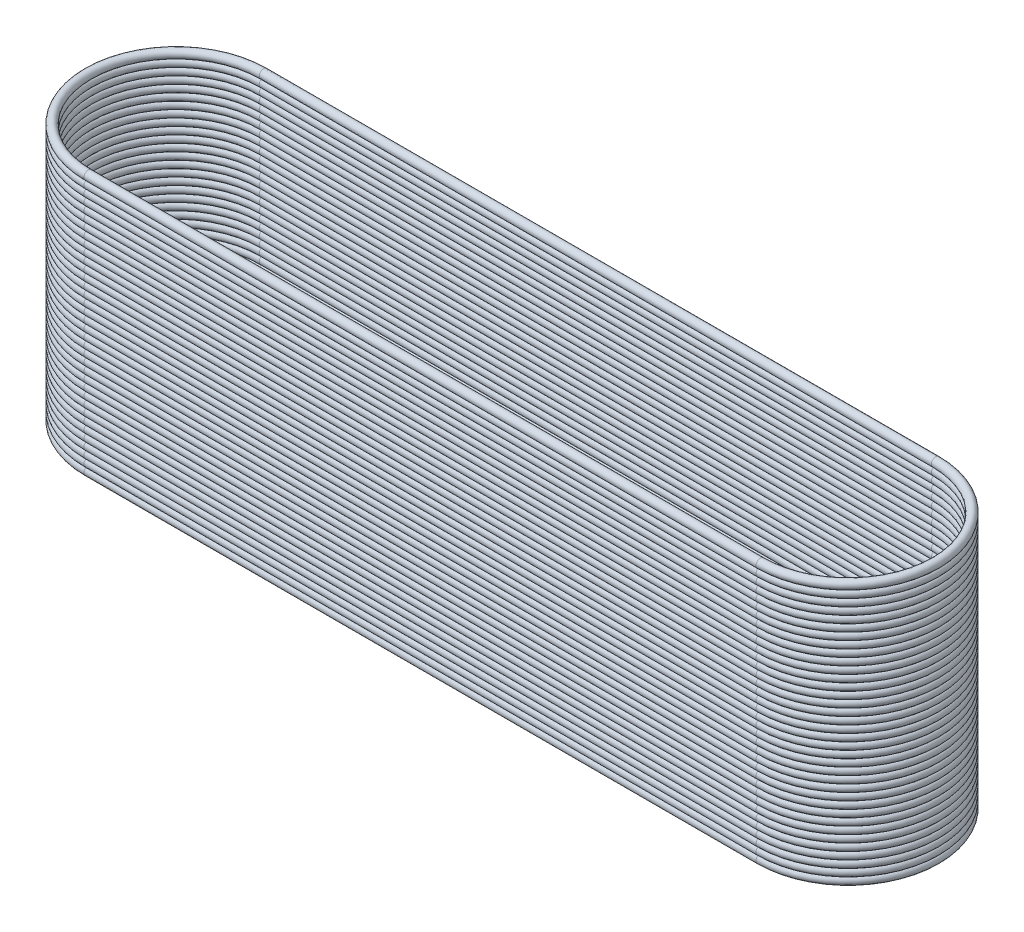
SolidWorks part; units mm, degrees
ref_plane "Front Plane" through (0, 0, 0) normal (0, 0, 1) x (1, 0, 0)
ref_plane "Top Plane" through (0, 0, 0) normal (0, 1, 0) x (1, 0, 0)
ref_plane "Right Plane" through (0, 0, 0) normal (1, 0, 0) x (0, 0, -1)
sketch "Sketch1" plane through (0, 0, 0) normal (0, 1, 0) x (1, 0, 0)
  line L0 (-11.5, 0) -> (11.5, 0) construction
  line L1 (-55, 0) -> (55, 0) construction
  line L2 (-11.5, 3) -> (11.5, 3)
  line L3 (-11.5, -3) -> (11.5, -3)
  arc A0 (-11.5, 3) -> (-11.5, -3) centre (-11.5, 0) ccw
  arc A1 (11.5, -3) -> (11.5, 3) centre (11.5, 0) ccw
  point P5 (0, 0)
  dimension "D2" = 3
  dimension "D1" = 23
sketch "Sketch2" plane through (0, 0, 0) normal (1, 0, 0) x (0, 0, -1)
  line L0 (3, 0) -> (-3, 0) construction
  line L1 (3, 0) -> (-3, 0) construction
  circle A0 centre (3, 0) radius 0.15
sweep "Sweep1" add profiles "Sketch2" path "Sketch1"
sketch "Sketch3" plane through (0, 0, 0) normal (0, 0, 1) x (1, 0, 0)
  line L0 (0, 0) -> (0, 1.9673) construction
pattern_linear "LPattern1" count 36 spacing 0.25 along (0, 1, 0) of "Sweep1"
